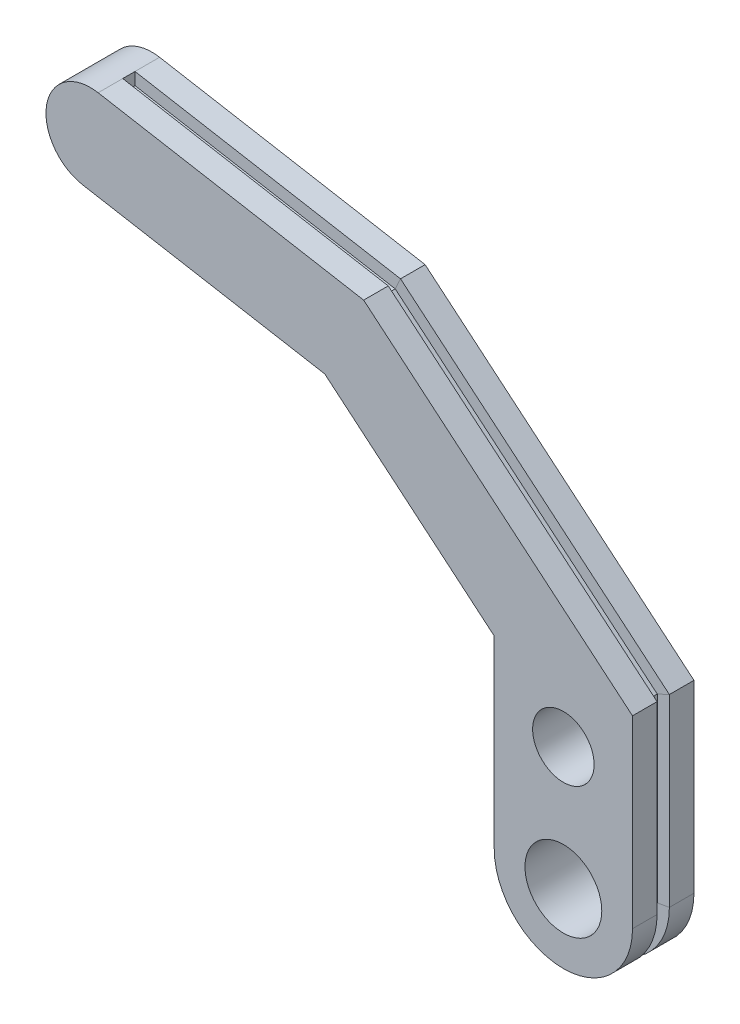
SolidWorks part; units mm, degrees
ref_plane "Front Plane" through (0, 0, 0) normal (0, 0, 1) x (1, 0, 0)
ref_plane "Top Plane" through (0, 0, 0) normal (0, 1, 0) x (1, 0, 0)
ref_plane "Right Plane" through (0, 0, 0) normal (1, 0, 0) x (0, 0, -1)
sketch "Sketch1" [suppressed] plane through (0, 0, 0) normal (0, 0, 1) x (1, 0, 0)
  line L0 (25.1277, -0.5112) -> (27.8541, 37.4911) construction
  line L1 (27.8541, 37.4911) -> (18.3535, 38.1727) construction
  line L2 (18.0023, 0) -> (20.7287, 38.0023) construction
  line L3 (18.3535, 38.1727) -> (15.6271, 0.1704) construction
  line L4 (4.5085, 0) -> (8.3185, 0) construction
  line L5 (-4.5085, 0) -> (4.5085, 0) construction
  line L6 (-4.5085, 0) -> (-4.5085, -50.8) construction
  line L7 (-4.5085, -50.8) -> (4.5085, -50.8) construction
  line L8 (4.5085, 0) -> (4.5085, -50.8) construction
  line L9 (8.3185, 0) -> (8.3185, -50.8) construction
  line L10 (8.3185, -50.8) -> (4.5085, -50.8) construction
  line L11 (15.6271, 0.1704) -> (25.1277, -0.5112) construction
  line L16 (-27.8541, 37.4911) -> (-18.3535, 38.1727) construction
  line L17 (0, 9.525) -> (0, -7.0986) construction
  line L18 (-18.3535, 38.1727) -> (-15.6271, 0.1704) construction
  line L19 (-15.6271, 0.1704) -> (-25.1277, -0.5112) construction
  line L20 (-25.1277, -0.5112) -> (-27.8541, 37.4911) construction
  line L21 (-18.9111, 12.6674) -> (18.9111, 12.6674) construction
  line L22 (-8.3185, -50.8) -> (-4.5085, -50.8) construction
  line L25 (-4.5085, 0) -> (-8.3185, 0) construction
  line L26 (-8.3185, 0) -> (-8.3185, -50.8) construction
  line L32 (-18.0023, 0) -> (-20.7287, 38.0023) construction
  line L48 (12.6181, 13.5168) -> (10.9227, 0.9555) construction
  line L49 (-12.6181, 13.5168) -> (-10.9227, 0.9555) construction
  circle A1 centre (18.0023, 0) radius 7.1438 construction
  circle A3 centre (18.9111, 12.6674) radius 6.35 construction
  circle A4 centre (-18.0023, 0) radius 7.1437 construction
  circle A5 centre (-18.9111, 12.6674) radius 6.35 construction
  point P0 (10.8585, 0)
  point P28 (0, 0)
  point P43 (25.146, 0)
  point P45 (-25.146, 0)
  dimension "D7" = 0
  dimension "D15" = 14.2875
  dimension "D13" = 12.7
  dimension "D14" = 12.7
  dimension "D2" = 2.54
  dimension "D3" = 9.525
  dimension "D4" = 38.1
  dimension "D5" = 16.637
  dimension "D6" = 50.8
  dimension "D8" = 3.81
sketch "Sketch3" plane through (0, 0, 0) normal (0, 0, 1) x (1, 0, 0)
  line L0 (0, 0) -> (0, 12.7) construction
  line L3 (7.1437, 19.05) -> (7.1437, 0)
  line L7 (-7.1438, 0) -> (-7.1438, 19.05)
  line L11 (-7.1438, 19.05) -> (-24.6555, 33.7441)
  line L12 (-24.6555, 33.7441) -> (-49.6696, 38.1548)
  line L13 (7.1437, 19.05) -> (-20.6374, 42.3611)
  line L14 (-20.6374, 42.3611) -> (-48.0749, 47.1991)
  line L15 (-42.439, 46.2053) -> (-44.0337, 37.161) construction
  line L16 (-13.6197, 36.4726) -> (-19.523, 29.4374) construction
  circle A0 centre (0, 0) radius 3.9688
  arc A1 (7.1437, 0) -> (-7.1438, 0) centre (0, 0) cw
  circle A2 centre (0, 12.7) radius 3.175
  circle A4 centre (0, 0) radius 7.1438 construction
  arc A11 (-48.0749, 47.1991) -> (-49.6696, 38.1548) centre (-48.8723, 42.6769) ccw
  dimension "D1" = 7.1437
  dimension "D2" = 14.2875
  dimension "D3" = 6.35
  dimension "D4" = 7.9375
  dimension "D5" = 12.7
  dimension "D6" = 180
  dimension "D7" = 22.86
  dimension "D8" = 130
  dimension "D9" = 25.4
  dimension "D10" = 150
  dimension "D11" = 6.35
  dimension "D15" = 6.35
extrude "Boss-Extrude1" add sketch "Sketch3" along normal blind 6.35
fillet "Fillet1" [suppressed] radius 2.54
ref_plane "Plane1" through (-48.0749, 0, 0) normal (1, 0, 0) x (0, 0, -1)
sketch "Sketch6" plane through (0, 0, 0) normal (0, 0, -1) x (-1, 0, 0)
  line L1 (20.6374, 42.3611) -> (48.0749, 47.1991) construction
  line L2 (-7.1437, 19.05) -> (20.6374, 42.3611) construction
  line L3 (-7.1437, 19.05) -> (20.6374, 42.3611)
  line L4 (-7.1437, 0) -> (-7.1437, 19.05) construction
  line L5 (-7.1437, 0) -> (-7.1437, 19.05)
  line L6 (20.6374, 42.3611) -> (48.0749, 47.1991)
  arc A0 (-7.1437, 0) -> (7.1438, 0) centre (0, 0) ccw construction
  arc A1 (-7.1437, 0) -> (7.1438, 0) centre (0, 0) ccw
sketch "Sketch4" plane through (-48.0749, 0, 0) normal (1, 0, 0) x (0, 0, -1)
  line L0 (-6.35, 47.1991) -> (0, 47.1991) construction
  line L1 (-3.81, 47.1991) -> (-2.54, 47.1991)
  line L2 (-3.81, 47.1991) -> (-3.81, 45.9291)
  line L3 (-3.81, 45.9291) -> (-2.54, 45.9291)
  line L4 (-2.54, 47.1991) -> (-2.54, 45.9291)
  point P6 (-3.175, 47.1991)
  dimension "D1" = 1.27
  dimension "D2" = 0.635
sweep "Cut-Sweep1" cut profiles "Sketch4" path "Sketch6"
